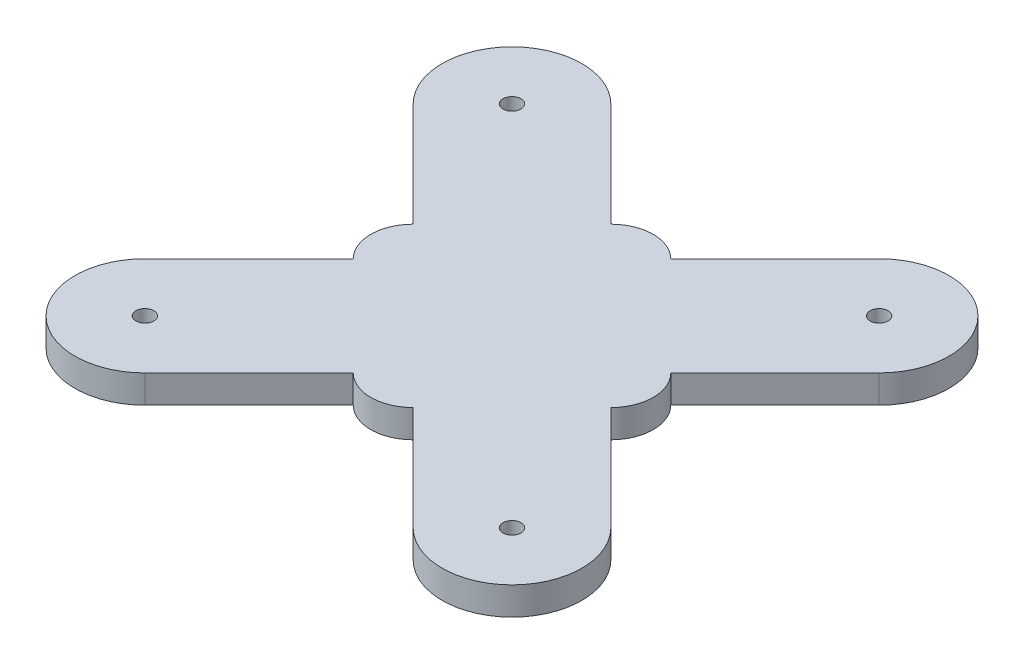
SolidWorks part; units mm, degrees
ref_plane "Front Plane" through (0, 0, 0) normal (0, 0, 1) x (1, 0, 0)
ref_plane "Top Plane" through (0, 0, 0) normal (0, 1, 0) x (1, 0, 0)
ref_plane "Right Plane" through (0, 0, 0) normal (1, 0, 0) x (0, 0, -1)
sketch "Sketch1" plane through (0, 0, 0) normal (0, 1, 0) x (1, 0, 0)
  line L0 (65.6549, -65.6549) -> (25.2437, -25.2437) construction
  line L1 (-65.6549, 65.6549) -> (-25.2437, 25.2437) construction
  line L2 (-47.9772, 83.3325) -> (-10.7192, 46.0745)
  line L3 (-83.3325, 47.9772) -> (-46.0745, 10.7192)
  line L4 (-65.6549, -65.6549) -> (-25.2437, -25.2437) construction
  line L5 (-65.6549, -65.6549) -> (-25.2437, -25.2437) construction
  line L6 (-83.3325, -47.9772) -> (-46.0745, -10.7192)
  line L7 (-47.9772, -83.3325) -> (-10.7192, -46.0745)
  line L8 (46.0745, -10.7192) -> (83.3325, -47.9772)
  line L9 (10.7192, 46.0745) -> (47.9772, 83.3325)
  line L10 (-25.2437, 25.2437) -> (-65.6549, 65.6549) construction
  line L11 (25.2437, -25.2437) -> (65.6549, -65.6549) construction
  line L12 (25.2437, 25.2437) -> (65.6549, 65.6549) construction
  line L13 (25.2437, 25.2437) -> (65.6549, 65.6549) construction
  line L14 (46.0745, 10.7192) -> (83.3325, 47.9772)
  line L15 (10.7192, -46.0745) -> (47.9772, -83.3325)
  line L16 (0, 150) -> (0, -150) construction
  circle A0 centre (0, 0) radius 150 construction
  circle A1 centre (-65.6549, 65.6549) radius 57.15 construction
  circle A2 centre (65.6549, -65.6549) radius 57.15 construction
  circle A3 centre (65.6549, 65.6549) radius 57.15 construction
  circle A4 centre (-65.6549, -65.6549) radius 57.15 construction
  arc A5 (-47.9772, 83.3325) -> (-83.3325, 47.9772) centre (-65.6549, 65.6549) ccw
  arc A6 (47.9772, -83.3325) -> (83.3325, -47.9772) centre (65.6549, -65.6549) ccw
  arc A7 (-83.3325, -47.9772) -> (-47.9772, -83.3325) centre (-65.6549, -65.6549) ccw
  arc A8 (83.3325, 47.9772) -> (47.9772, 83.3325) centre (65.6549, 65.6549) ccw
  arc A9 (10.7192, 46.0745) -> (-10.7192, 46.0745) centre (0, 35.3553) ccw
  arc A10 (46.0745, -10.7192) -> (46.0745, 10.7192) centre (35.3553, 0) ccw
  arc A11 (-10.7192, -46.0745) -> (10.7192, -46.0745) centre (0, -35.3553) ccw
  arc A12 (-46.0745, 10.7192) -> (-46.0745, -10.7192) centre (-35.3553, 0) ccw
  circle A13 centre (-65.6549, 65.6549) radius 3.2
  circle A14 centre (65.6549, -65.6549) radius 3.2
  circle A15 centre (65.6549, 65.6549) radius 3.2
  circle A16 centre (-65.6549, -65.6549) radius 3.2
  point P3 (0, 0)
  point P16 (0, 0)
extrude "Boss-Extrude1" add sketch "Sketch1" along normal blind 10
